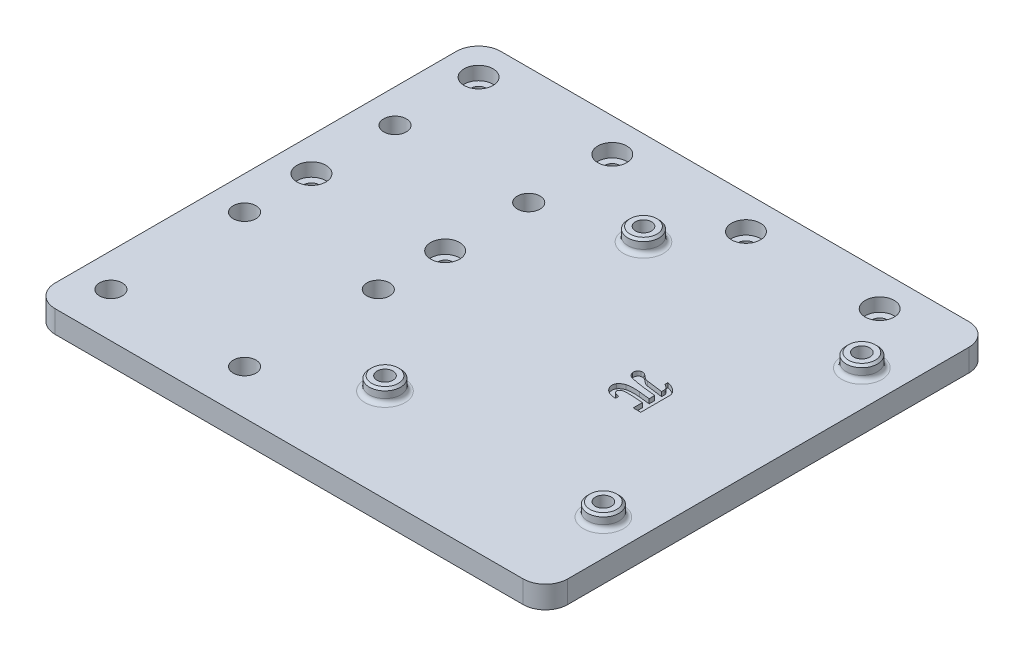
SolidWorks part; units mm, degrees
ref_plane "Front Plane" through (0, 0, 0) normal (0, 0, 1) x (1, 0, 0)
ref_plane "Top Plane" through (0, 0, 0) normal (0, 1, 0) x (1, 0, 0)
ref_plane "Right Plane" through (0, 0, 0) normal (1, 0, 0) x (0, 0, -1)
sketch "Sketch1" plane through (0, 0, 0) normal (0, 1, 0) x (1, 0, 0)
  line L1 (0, 0) -> (65, 0)
  line L2 (0, 0) -> (0, -100)
  line L3 (0, -100) -> (65, -100)
  line L4 (65, 0) -> (65, -100)
  dimension "D1" = 65
  dimension "D2" = 100
extrude "Boss-Extrude1" add sketch "Sketch1" along normal blind 5
sketch "Sketch2" plane through (0, 5, 0) normal (0, 1, 0) x (1, 0, 0)
  line L0 (32.5, 0) -> (32.5, -13.391) construction
  line L1 (8, -21) -> (57, -21) construction
  line L2 (8, -21) -> (8, -79) construction
  line L3 (8, -79) -> (57, -79) construction
  line L4 (57, -21) -> (57, -79) construction
  line L5 (65, 0) -> (0, 0) construction
  line L6 (32.5, -21) -> (32.5, -41.8005) construction
  line L7 (0, -50) -> (9.0135, -50) construction
  line L8 (0, 0) -> (0, -100) construction
  circle A0 centre (8, -21) radius 3.5
  circle A1 centre (57, -21) radius 3.5
  circle A2 centre (57, -79) radius 3.5
  circle A3 centre (8, -79) radius 3.5
  point P11 (8, -21)
  point P12 (57, -21)
  point P13 (57, -79)
  point P14 (8, -79)
  point P19 (8, -50)
  dimension "D3" = 7
  dimension "D1" = 58
  dimension "D2" = 49
extrude "Boss-Extrude2" add sketch "Sketch2" along normal blind 3
sketch "Sketch3" plane through (0, 8, 0) normal (0, 1, 0) x (1, 0, 0)
  point P0 (8, -21)
  point P1 (57, -21)
  point P3 (57, -79)
  point P5 (8, -79)
hole_wizard "Ø3.6 (3.6) Diameter Hole1" positions "Sketch3" profile "Sketch4" hole size "Ø3.6" standard "ANSI Metric" end condition up to next
sketch "Sketch4" plane through (8, 8, 21) normal (1, 0, 0) x (0, 0, 1)
  line L0 (0, 0) -> (0, 8)
  line L1 (0, 8) -> (1.8, 8)
  line L2 (1.8, 8) -> (1.8, 0)
  line L5 (1.8, 0) -> (0, 0)
  line L11 (0, -6.35) -> (0, 107.95) construction
  dimension "Thru Hole Dia." = 3.6
  dimension "Thru Hole Depth" = 8
chamfer "Chamfer1" [suppressed] distance 0.5 angle 45
sketch "Sketch5" plane through (0, 5, 0) normal (0, 1, 0) x (1, 0, 0)
  line L0 (32.5, 0) -> (32.5, -29.0521) construction
  line L1 (65, 0) -> (0, 0) construction
  line L2 (17.5, -7.5) -> (47.5, -7.5) construction
  point P7 (32.5, -7.5)
  dimension "D1" = 7.5
  dimension "D2" = 30
hole_wizard "CBORE for M3 SHCS1" positions "Sketch8" profile "Sketch7" counterbore size "M3" standard "ANSI Metric" end condition up to next
sketch "Sketch8" plane through (0, 5, 0) normal (0, 1, 0) x (1, 0, 0)
  point P0 (17.5, -7.5)
  point P3 (47.5, -7.5)
sketch "Sketch7" plane through (17.5, 5, 7.5) normal (1, 0, 0) x (0, 0, 1)
  line L0 (0, 0) -> (0, 5)
  line L1 (0, 5) -> (1.7, 5)
  line L3 (1.7, 5) -> (1.7, 3)
  line L4 (1.7, 3) -> (3.25, 3)
  line L5 (3.25, 3) -> (3.25, 0)
  line L7 (3.25, 0) -> (0, 0)
  line L11 (0, -6.35) -> (0, 107.95) construction
  dimension "Thru Hole Dia." = 3.4
  dimension "Thru Hole Depth" = 5
  dimension "C'Bore Dia." = 6.5
  dimension "C'Bore Depth" = 3
sketch "Sketch9" plane through (0, 0, 0) normal (-1, 0, 0) x (0, 0, 1)
  line L0 (0, 0) -> (100, 0) construction
  line L1 (0, 5) -> (100, 5)
  line L2 (0, 5) -> (0, 0)
  line L3 (0, 0) -> (100, 0)
  line L4 (100, 5) -> (100, 0)
  dimension "D1" = 100
extrude "Boss-Extrude3" add sketch "Sketch9" along normal blind 50
sketch "Sketch11" plane through (0, 5, 0) normal (0, 1, 0) x (1, 0, 0)
  line L0 (17.5, -7.5) -> (-50, -7.5) construction
  line L1 (-50, -100) -> (-50, 0) construction
  line L4 (-12.5, -7.5) -> (-12.5, -45) construction
  line L6 (-42.5, -7.5) -> (-42.5, -45) construction
  point P6 (-12.5, -7.5)
  point P7 (-42.5, -7.5)
  point P20 (-12.5, -45)
  point P23 (-42.5, -45)
hole_wizard "CBORE for M3 SHCS2" positions "Sketch11" profile "Sketch12" counterbore size "M3" standard "ANSI Metric" end condition up to next
sketch "Sketch12" plane through (-42.5, 5, 45) normal (1, 0, 0) x (0, 0, 1)
  line L0 (0, 0) -> (0, 5)
  line L1 (0, 5) -> (1.7, 5)
  line L3 (1.7, 5) -> (1.7, 3)
  line L4 (1.7, 3) -> (3.25, 3)
  line L5 (3.25, 3) -> (3.25, 0)
  line L7 (3.25, 0) -> (0, 0)
  line L11 (0, -6.35) -> (0, 107.95) construction
  dimension "Thru Hole Dia." = 3.4
  dimension "Thru Hole Depth" = 5
  dimension "C'Bore Dia." = 6.5
  dimension "C'Bore Depth" = 3
sketch "Sketch13" plane through (0, 5, 0) normal (0, 1, 0) x (1, 0, 0)
  line L0 (-42.5, -7.5) -> (-12.5, -7.5) construction
  line L1 (-42.5, -60) -> (-12.5, -60) construction
  line L2 (-42.5, -60) -> (-42.5, -90) construction
  line L3 (-42.5, -90) -> (-12.5, -90) construction
  line L4 (-12.5, -60) -> (-12.5, -90) construction
  line L5 (-27.5, -7.5) -> (-27.5, -23.5345) construction
  line L6 (-42.5, -7.5) -> (-42.5, -45) construction
  line L8 (-42.5, -26.25) -> (-12.5, -26.25) construction
  line L10 (-12.5, -7.5) -> (-12.5, -45) construction
  circle A0 centre (-12.5, -45) radius 1.7 construction
  point P10 (-27.5, -60)
  point P15 (-12.5, -60)
  point P18 (-12.5, -90)
  point P21 (-42.5, -90)
  point P24 (-42.5, -60)
  point P41 (-42.5, -26.25)
  point P44 (-12.5, -26.25)
  dimension "D1" = 30
  dimension "D2" = 15
hole_wizard "Ø5.1 (5.1) Diameter Hole1" positions "Sketch13" profile "Sketch14" hole size "Ø5.1" standard "ANSI Metric" end condition up to next
sketch "Sketch14" plane through (-12.5, 5, 26.25) normal (1, 0, 0) x (0, 0, 1)
  line L0 (0, 0) -> (0, 5)
  line L1 (0, 5) -> (2.55, 5)
  line L2 (2.55, 5) -> (2.55, 0)
  line L5 (2.55, 0) -> (0, 0)
  line L11 (0, -6.35) -> (0, 107.95) construction
  dimension "Thru Hole Dia." = 5.1
  dimension "Thru Hole Depth" = 5
sketch "Sketch16" plane through (0, 5, 0) normal (0, 1, 0) x (1, 0, 0)
  line L0 (8, -21) -> (57, -21) construction
  line L1 (8, -79) -> (57, -79) construction
  line L2 (32.5, -21) -> (32.5, -79) construction
  text T0 "<b>π</b>\r\n" font "Arial Rounded MT Bold" height in points 48
extrude "Cut-Extrude1" cut sketch "Sketch16" against normal blind 1
fillet "Fillet1" radius 1 4 edges at (8, 5, 82.5) (8, 5, 24.5) (57, 5, 24.5) (57, 5, 82.5)
fillet "Fillet2" radius 5 4 edges at (65, 2.5, 100) (65, 2.5, 0) (-50, 2.5, 0) (-50, 2.5, 100)
chamfer "Chamfer2" distance 0.5 angle 45 4 edges at (57, 8, 24.5) (57, 8, 82.5) (8, 8, 82.5) (8, 8, 24.5)
equation "\"D2@Sketch11\"=\"D1@Sketch11\""
